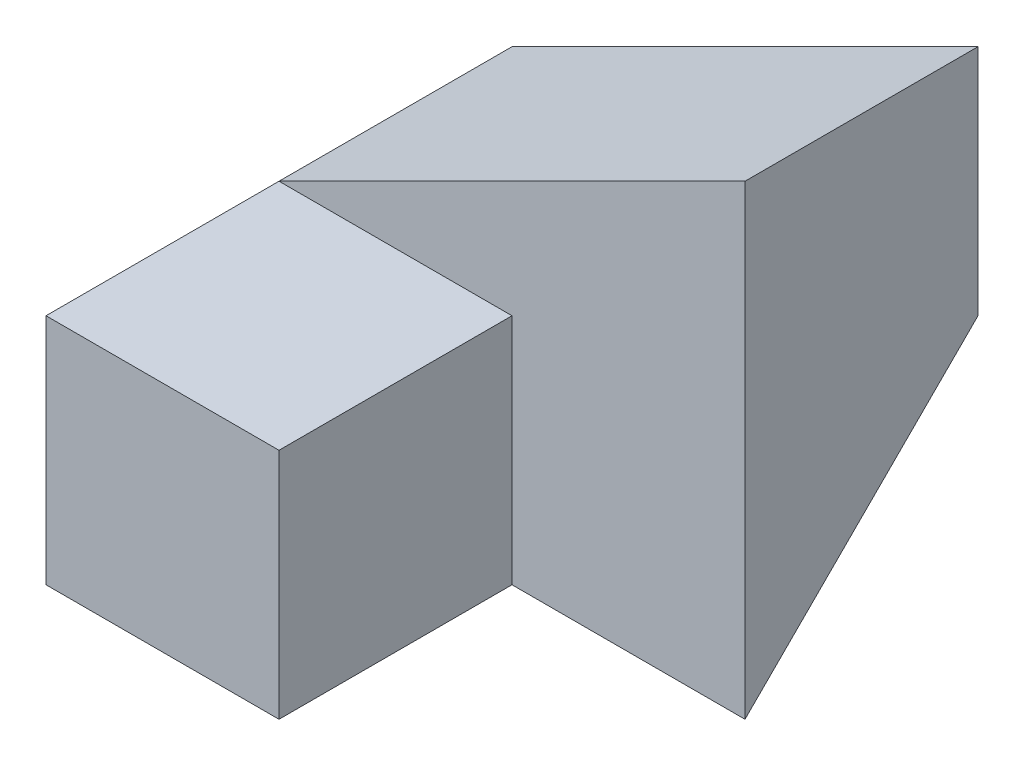
SolidWorks part; units mm, degrees
ref_plane "Front Plane" through (0, 0, 0) normal (0, 0, 1) x (1, 0, 0)
ref_plane "Top Plane" through (0, 0, 0) normal (0, 1, 0) x (1, 0, 0)
ref_plane "Right Plane" through (0, 0, 0) normal (1, 0, 0) x (0, 0, -1)
sketch "Sketch1" plane through (0, 0, 0) normal (0, 0, 1) x (1, 0, 0)
  line L1 (0, 0) -> (40, 0)
  line L2 (0, 0) -> (0, 40)
  line L3 (0, 40) -> (40, 40)
  line L4 (40, 0) -> (40, 40)
  dimension "D1" = 40
  dimension "D2" = 40
extrude "Boss-Extrude1" add sketch "Sketch1" along normal blind 40
sketch "Sketch2" plane through (0, 0, 40) normal (0, 0, 1) x (1, 0, 0)
  line L0 (40, 40) -> (0, 20)
  line L1 (0, 20) -> (0, 40)
  line L2 (0, 40) -> (40, 40)
  dimension "D1" = 20
extrude "Cut-Extrude1" cut sketch "Sketch2" against normal blind 40
sketch "Sketch3" plane through (40, 0, 0) normal (1, 0, 0) x (0, 0, -1)
  line L1 (-40, 40) -> (-20, 40)
  line L2 (-40, 40) -> (-40, 20)
  line L3 (-40, 20) -> (-20, 20)
  line L4 (-20, 40) -> (-20, 20)
  dimension "D1" = 20
  dimension "D2" = 20
extrude "Cut-Extrude2" cut sketch "Sketch3" against normal blind 40
sketch "Sketch5" plane through (0, 20, 0) normal (0, 1, 0) x (1, 0, 0)
  line L0 (0, -20) -> (40, -20) construction
  line L1 (20, -20) -> (40, -20)
  line L2 (20, -20) -> (20, -40)
  line L3 (20, -40) -> (40, -40)
  line L4 (40, -20) -> (40, -40)
extrude "Cut-Extrude4" cut sketch "Sketch5" against normal blind 40
sketch "Sketch6" plane through (0, 0, 0) normal (-1, 0, 0) x (0, 0, 1)
  line L0 (0, 20) -> (20, 0)
  line L1 (40, 0) -> (0, 0) construction
  line L2 (20, 0) -> (0, 0)
  line L3 (0, 0) -> (0, 20)
extrude "Cut-Extrude5" cut sketch "Sketch6" against normal blind 40
